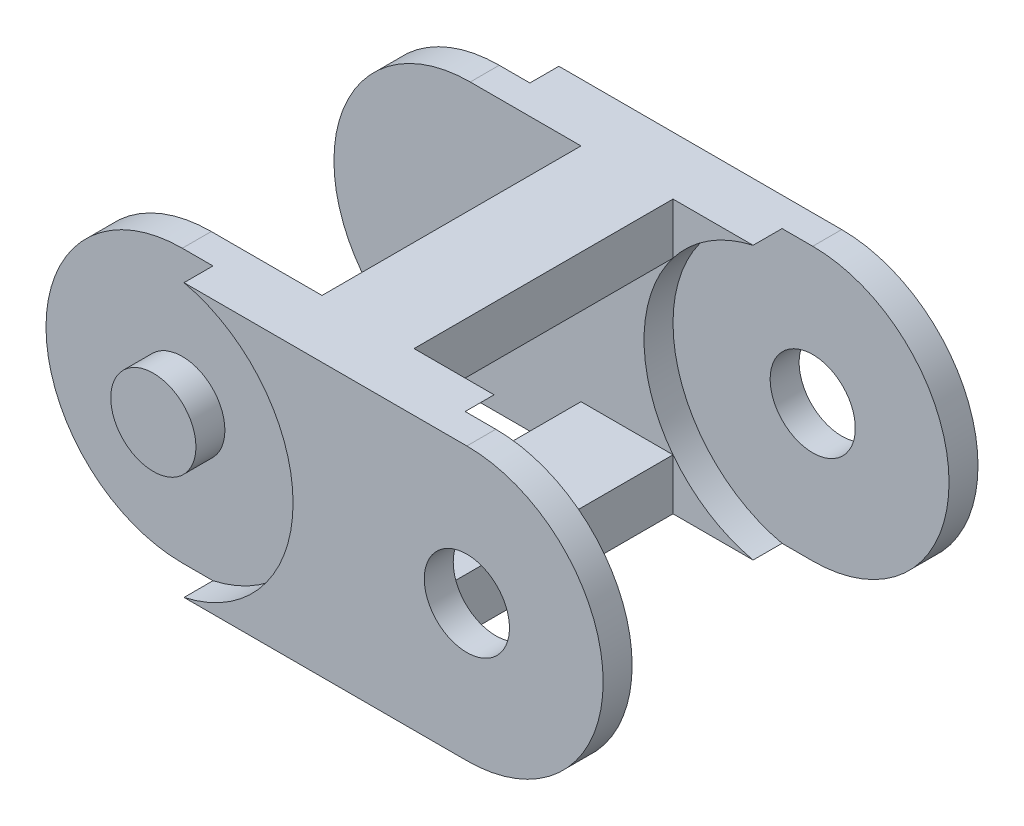
SolidWorks part; units mm, degrees
material "Нейлон"
ref_plane "Front" through (0, 0, 0) normal (0, 0, 1) x (1, 0, 0)
ref_plane "Top" through (0, 0, 0) normal (0, 1, 0) x (1, 0, 0)
ref_plane "Right" through (0, 0, 0) normal (1, 0, 0) x (0, 0, -1)
sketch "Sketch1" plane through (0, 0, 0) normal (0, 0, 1) x (1, 0, 0)
  line L0 (-23, 0) -> (23, 0) construction
  line L1 (-23, 20) -> (23, 20)
  line L2 (-23, -20) -> (23, -20)
  arc A0 (-23, 20) -> (-23, -20) centre (-23, 0) ccw
  arc A1 (23, -20) -> (23, 20) centre (23, 0) ccw
  point P3 (0, 0)
extrude "Boss-Extrude1" add sketch "Sketch1" along normal blind 8.5
sketch "Sketch2" plane through (0, 0, 0) normal (0, 0, -1) x (-1, 0, 0)
  arc A0 (-23, 20) -> (-23, -20) centre (-23, 0) ccw construction
  circle A1 centre (-23, 0) radius 20.5
  dimension "D1" = 0.5
extrude "Cut-Extrude1" cut sketch "Sketch2" against normal blind 4.25
sketch "Sketch3" plane through (0, 0, 8.5) normal (0, 0, 1) x (1, 0, 0)
  circle A0 centre (-23, 0) radius 20.5
  arc A2 (-23, 20) -> (-23, -20) centre (-23, 0) ccw construction
  dimension "D1" = 0.5
extrude "Cut-Extrude2" cut sketch "Sketch3" against normal blind 4.25
sketch "Sketch4" plane through (0, 0, 4.25) normal (0, 0, -1) x (-1, 0, 0)
  circle A0 centre (-23, 0) radius 6.25
extrude "Cut-Extrude3" cut sketch "Sketch4" against normal through all
sketch "Sketch5" plane through (0, 0, 4.25) normal (0, 0, 1) x (1, 0, 0)
  circle A0 centre (-23, 0) radius 6.25
extrude "Boss-Extrude2" add sketch "Sketch5" along normal up to surface (4.25 mm away)
sketch "Sketch6" plane through (0, 0, 0) normal (0, 0, -1) x (-1, 0, 0)
  line L0 (-23, 20) -> (18.5, 20) construction
  line L1 (-6.7519, 12.5) -> (6.7519, 12.5)
  line L2 (-6.7519, 12.5) -> (-6.7519, 20)
  line L3 (-6.7519, 20) -> (6.7519, 20)
  line L4 (6.7519, 12.5) -> (6.7519, 20)
  line L5 (-6.7519, 12.5) -> (6.7519, 20) construction
  line L6 (-6.7519, 20) -> (6.7519, 12.5) construction
  line L7 (-18.5, 20) -> (23, 20) construction
  line L8 (0, 0) -> (5.2998, 0) construction
  line L9 (-6.7519, -12.5) -> (6.7519, -12.5) construction
  arc A0 (-18.5, -20) -> (-18.5, 20) centre (-23, 0) ccw construction
  point P0 (0, 16.25)
extrude "Boss-Extrude3" add sketch "Sketch6" along normal blind 38
mirror "Mirror1" about plane through (0, 0, 0) normal (0, 1, 0) of "Boss-Extrude3"
ref_plane "Plane1" through (0, 0, -19) normal (0, 0, 1) x (1, 0, 0)
mirror "Зеркальное отражение1" about plane through (0, 0, -19) normal (0, 0, 1)
equation "\"H\"= 40"
equation "\"D1@Sketch1\"=\"H\""
equation "\"Ba\"= 74"
equation "\"Bi\"= 57"
equation "\"Hi\"= 25"
equation "\"L\"= 46"
equation "\"D2@Sketch1\"=\"L\""
equation "\"D\"= \"Hi\" / 2"
equation "\"D1@Sketch4\"=\"D\""
equation "\"D1@Sketch5\"=\"D\""
equation "\"thinkes1\"= ( \"Ba\" - \"Bi\" ) / 2"
equation "\"D1@Boss-Extrude1\"=\"thinkes1\""
equation "\"D1@Cut-Extrude1\"=\"thinkes1\"/2"
equation "\"D1@Cut-Extrude2\"=\"thinkes1\"/2"
equation "\"D1@Boss-Extrude3\"=\"Bi\""
equation "\"D1@Sketch6\"=\"Hi\""
equation "\"th2\"= 0.5"
equation "\"D1@Sketch2\"=\"th2\""
equation "\"D1@Sketch3\"=\"th2\""
